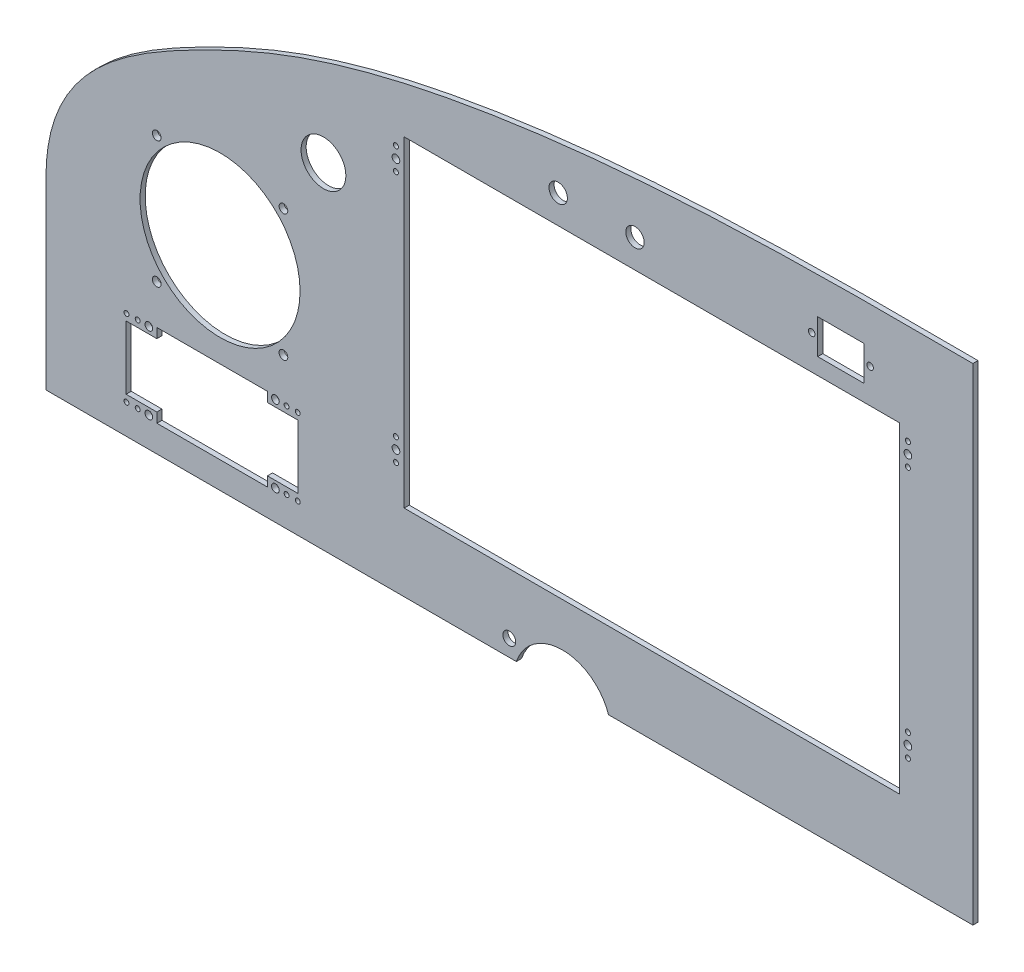
SolidWorks part; units mm, degrees
material "1060-H14"
ref_plane "Front Plane" through (0, 0, 0) normal (0, 0, 1) x (1, 0, 0)
ref_plane "Top Plane" through (0, 0, 0) normal (0, 1, 0) x (1, 0, 0)
ref_plane "Right Plane" through (0, 0, 0) normal (1, 0, 0) x (0, 0, -1)
sketch "Sketch1" plane through (0, 0, 0) normal (0, 0, 1) x (1, 0, 0)
  line L11 (-117.2518, -41.1401) -> (289.0537, -32.3757) construction
  line L12 (12.4666, -16.0047) -> (-220.8959, -16.0047)
  line L13 (58.1866, -16.0047) -> (238.9473, -16.0047)
  line L14 (238.9473, -16.0047) -> (238.9473, 225.2953)
  line L16 (-166.3344, 43.9076) -> (214.5625, 52.7724) construction
  line L18 (-220.8959, -16.0047) -> (-220.8959, 75.746)
  arc A7 (12.4666, -16.0047) -> (58.1866, -16.0047) centre (35.3266, -23.6819) cw
  circle A8 centre (8.9512, -7.8001) radius 3.175
  spline S0 degree 3 poles (238.9473, 225.2953) (159.1857, 225.7993) (43.8738, 224.9903) (-86.6412, 195.7232) (-170.078, 157.1798) (-220.8328, 123.6125) (-220.8959, 75.746) knots 0 0 0 0 0.463494 0.667883 0.767851 1 1 1 1
  dimension "D3" = 381
  dimension "D5" = 406.4
  dimension "D2" = 6.35
  dimension "D1" = 241.3
  dimension "D4" = 233.3625
  dimension "D6" = 180.7606
  dimension "D7" = 45.72
extrude "Boss-Extrude1" add sketch "Sketch1" along normal blind 2.54
sketch "Cutouts" plane through (0, 0, 2.54) normal (0, 0, 1) x (1, 0, 0)
  line L0 (57.1239, -14.1451) -> (223.9618, -14.1451) construction
  line L11 (550.6278, 1448.8605) -> (3233.1045, 1448.8605) construction
  line L12 (223.9618, -14.1451) -> (223.9618, 222.0749) construction
  line L13 (-162.1683, 45.1669) -> (244.1923, 50.8314) construction
  line L14 (58.1866, -16.0047) -> (238.9473, -16.0047) construction
  line L15 (-220.8959, 75.746) -> (-220.8959, -16.0047) construction
  line L16 (-220.8959, -16.0047) -> (12.4666, -16.0047) construction
  circle A35 centre (-83.2509, 150.4499) radius 11.1125
  circle A37 centre (33.21, 195.7539) radius 4.572
  circle A38 centre (71.31, 195.7539) radius 4.572
  point P2 (-284.8883, -94.1836)
  point P6 (-130.32, 79.2722)
  point P16 (-139.867, 149.4505)
  point P19 (0, 0)
  point P22 (0, 0)
  line B0 (158.9576, 198.613) -> (161.9675, 198.613) construction
  line B1 (161.9675, 189.7623) -> (161.9675, 206.9073)
  line B2 (161.9675, 189.7623) -> (184.9545, 189.7623)
  line B3 (184.9545, 189.7623) -> (184.9545, 206.9073)
  line B4 (161.9675, 206.9073) -> (184.9545, 206.9073)
  line B5 (187.9644, 198.613) -> (184.9545, 198.613) construction
  circle B6 centre (158.9576, 198.613) radius 1.6319
  circle B7 centre (187.9644, 198.613) radius 1.6319
  line B8 (-45.3784, 170.1773) -> (-43.2194, 170.1773) construction
  line B9 (-43.2194, 181.6073) -> (202.6526, 181.6073)
  line B10 (-43.2194, 181.6073) -> (-43.2194, 22.0953)
  line B11 (-43.2194, 22.0953) -> (202.6526, 22.0953)
  line B12 (202.6526, 181.6073) -> (202.6526, 22.0953)
  line B13 (204.8116, 170.1773) -> (202.6526, 170.1773) construction
  line B14 (-47.2834, 175.7273) -> (-47.2834, 170.1773) construction
  line B15 (-47.2834, 170.1773) -> (-47.2834, 164.6273) construction
  line B16 (-47.2834, 164.6273) -> (-47.2834, 170.1773)
  line B17 (-47.2834, 50.7593) -> (-47.2834, 45.2093) construction
  line B18 (-47.2834, 45.2093) -> (-47.2834, 39.6593) construction
  line B19 (-47.2834, 39.6593) -> (-47.2834, 45.2093)
  line B20 (-60.6184, 17.0153) -> (-60.6184, 186.6873) construction
  line B21 (-60.6184, 186.6873) -> (220.0516, 186.6873) construction
  line B22 (220.0516, 186.6873) -> (220.0516, 17.0153) construction
  line B23 (220.0516, 17.0153) -> (-60.6184, 17.0153) construction
  line B24 (80.0944, 170.1773) -> (82.2534, 170.1773) construction
  line B25 (206.7166, 175.7273) -> (206.7166, 170.1773) construction
  line B26 (206.7166, 170.1773) -> (206.7166, 164.6273) construction
  line B27 (206.7166, 164.6273) -> (206.7166, 170.1773) construction
  line B28 (79.4832, 45.2093) -> (81.6422, 45.2093) construction
  line B29 (206.7166, 50.7593) -> (206.7166, 45.2093) construction
  line B30 (206.7166, 45.2093) -> (206.7166, 39.6593) construction
  line B31 (206.7166, 39.6593) -> (206.7166, 45.2093)
  circle B32 centre (206.7166, 170.1773) radius 1.905
  circle B33 centre (-47.2834, 170.1773) radius 1.905
  circle B34 centre (-47.2834, 45.2093) radius 1.905
  circle B35 centre (206.7166, 45.2093) radius 1.905
  circle B36 centre (-47.2834, 175.7273) radius 1.2446
  circle B37 centre (-47.2834, 164.6273) radius 1.2446
  circle B38 centre (-47.2834, 50.7593) radius 1.2446
  circle B39 centre (-47.2834, 39.6593) radius 1.2446
  circle B40 centre (206.7166, 175.7273) radius 1.2446
  circle B41 centre (206.7166, 164.6273) radius 1.2446
  circle B42 centre (206.7166, 50.7593) radius 1.2446
  circle B43 centre (206.7166, 39.6593) radius 1.2446
  line B44 (-95.7994, 33.5353) -> (-95.7994, 2.0393)
  line B45 (-95.7994, 33.5353) -> (-111.0394, 33.5353)
  line B46 (-111.0394, 33.5353) -> (-111.0394, 38.3613)
  line B47 (-111.0394, 38.3613) -> (-165.9034, 38.3613)
  line B48 (-165.9034, 38.3613) -> (-165.9034, 33.5353)
  line B49 (-165.9034, 33.5353) -> (-181.1434, 33.5353)
  line B50 (-181.1434, 33.5353) -> (-181.1434, 2.0393)
  line B51 (-181.1434, 2.0393) -> (-165.9034, 2.0393)
  line B52 (-165.9034, 2.0393) -> (-165.9034, -2.7867)
  line B53 (-165.9034, -2.7867) -> (-111.0394, -2.7867)
  line B54 (-111.0394, -2.7867) -> (-111.0394, 2.0393)
  line B55 (-111.0394, 2.0393) -> (-95.7994, 2.0393)
  line B56 (-108.982, -1.2627) -> (-111.0394, -1.2627) construction
  line B57 (-107.7886, 36.8373) -> (-109.846, 36.8373) construction
  circle B58 centre (-169.8658, 36.8373) radius 1.905
  circle B59 centre (-107.077, -1.2627) radius 1.905
  circle B60 centre (-107.077, 36.8373) radius 1.905
  circle B61 centre (-175.403, 36.8373) radius 1.2192
  circle B62 centre (-180.9656, 36.8373) radius 1.2192
  circle B63 centre (-169.8658, -1.2627) radius 1.905
  circle B64 centre (-175.403, -1.2627) radius 1.2192
  circle B65 centre (-180.9656, -1.2627) radius 1.2192
  circle B66 centre (-101.5398, -1.2627) radius 1.2192
  circle B67 centre (-95.9772, -1.2627) radius 1.2192
  circle B68 centre (-101.5398, 36.8373) radius 1.2192
  circle B69 centre (-95.9772, 36.8373) radius 1.2192
  line B70 (-316.6177, 48.904) -> (-234.0677, 48.904)
  line B71 (-316.6177, 48.904) -> (-316.6177, -1.896)
  line B72 (-316.6177, -1.896) -> (-234.0677, -1.896)
  line B73 (-234.0677, 48.904) -> (-234.0677, -1.896)
  circle B74 centre (-103.1034, 57.9728) radius 2.159
  circle B75 centre (-134.5359, 89.4053) radius 39.6875
  circle B76 centre (-165.9684, 57.9728) radius 2.159
  circle B77 centre (-103.1034, 120.8378) radius 2.159
  circle B78 centre (-165.9684, 120.8378) radius 2.159
  dimension "D3" = 38.1
  dimension "D4" = 86.36
  dimension "D5" = 22.225
  dimension "D6" = 9.144
  dimension "D7" = 105.41
  dimension "D1" = 38.1
  dimension "D2" = 406.4
sketch_block_instance "USB Block-1"
sketch_block "USB Block" parameters "D3"=3.2639, "D1"=17.145, "D2"=22.987, "D4"=3.0099, "D5"=8.2943
sketch_block_instance "HDX Block-1"
sketch_block "HDX Block" parameters "D1"=3.81, "D11"=2.4892, "D13"=2.4892, "D15"=2.4892, "D18"=2.4892, "D2"=124.968, "D3"=11.43, "D4"=159.512, "D5"=245.872, "D6"=254, "D7"=280.67, "D8"=169.672, "D9"=5.08, "D10"=17.399, "D12"=11.1, "D14"=11.1, "D16"=11.1, "D17"=5.55, "D19"=11.1, "D20"=5.55, "D21"=5.08
sketch_block_instance "Button Panel-1"
sketch_block "Button Panel" parameters "D7"=2.4384, "D14"=3.81, "D1"=85.344, "D2"=31.496, "D3"=38.1, "D4"=62.7888, "D5"=5.5372, "D6"=5.5626, "D8"=5.5372, "D9"=5.5626, "D10"=5.5372, "D11"=5.5372, "D12"=4.826, "D13"=3.302
sketch_block_instance "Electroair-1"
sketch_block "Electroair" parameters "D1"=82.55, "D2"=50.8
sketch_block_instance "Standard Inst-1"
sketch_block "Standard Inst"
extrude "Cut-Extrude2" cut sketch "Cutouts" against normal blind 2.54
